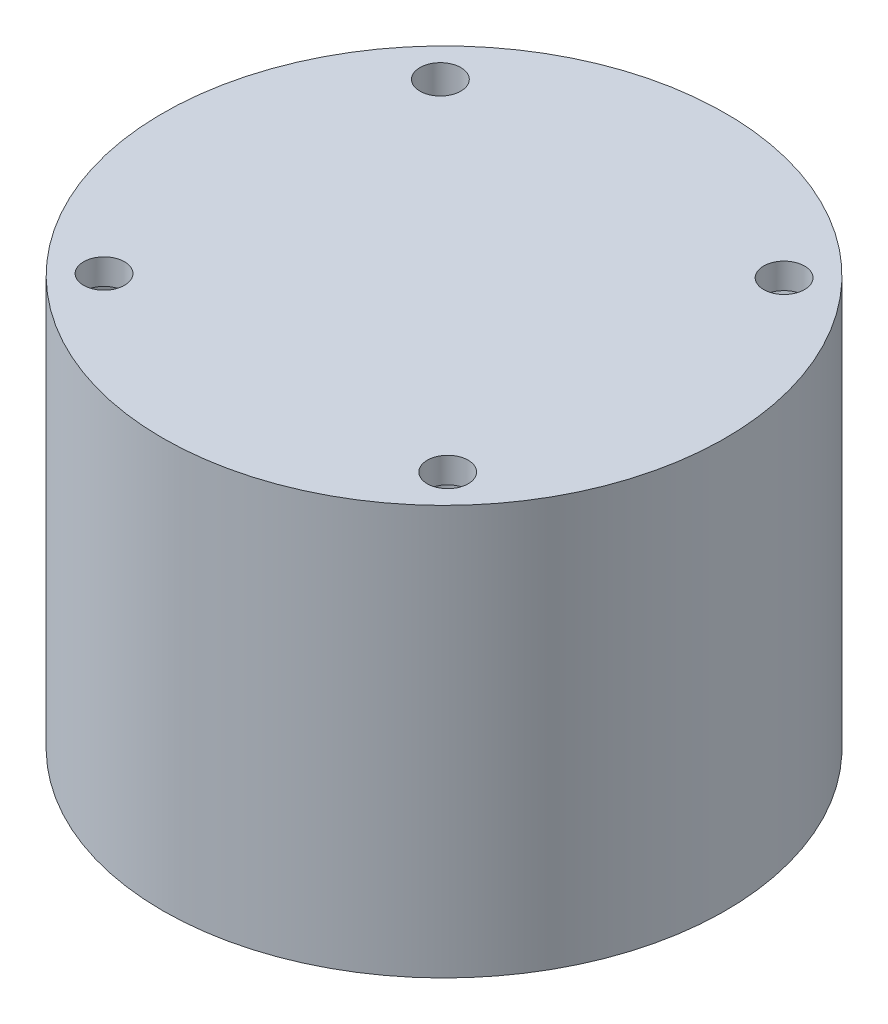
SolidWorks part; units mm, degrees
ref_plane "Спереди" through (0, 0, 0) normal (0, 0, 1) x (1, 0, 0)
ref_plane "Сверху" through (0, 0, 0) normal (0, 1, 0) x (1, 0, 0)
ref_plane "Справа" through (0, 0, 0) normal (1, 0, 0) x (0, 0, -1)
sketch "Эскиз1" plane through (0, 0, 0) normal (0, 1, 0) x (1, 0, 0)
  circle A0 centre (0, 0) radius 55
  dimension "D1" = 110
extrude "Бобышка-Вытянуть1" add sketch "Эскиз1" along normal blind 80
sketch "Эскиз2" plane through (0, 0, 0) normal (0, -1, 0) x (1, 0, 0)
  circle A0 centre (0, 0) radius 50
  dimension "D1" = 100
extrude "Вырез-Вытянуть1" cut sketch "Эскиз2" against normal blind 75
sketch "Эскиз3" plane through (0, 75, 0) normal (0, -1, 0) x (1, 0, 0)
  line L1 (-16.75, -7.5) -> (16.75, -7.5)
  line L2 (-16.75, -7.5) -> (-16.75, 7.5)
  line L3 (-16.75, 7.5) -> (16.75, 7.5)
  line L4 (16.75, -7.5) -> (16.75, 7.5)
  line L5 (-16.75, -7.5) -> (16.75, 7.5) construction
  line L6 (-16.75, 7.5) -> (16.75, -7.5) construction
  point P0 (0, 0)
  dimension "D1" = 15
  dimension "D2" = 33.5
extrude "Вырез-Вытянуть2" cut sketch "Эскиз3" against normal through all
sketch "Эскиз4" plane through (0, 80, 0) normal (0, 1, 0) x (1, 0, 0)
  line L0 (-16.75, 20.5) -> (-16.75, -20.5) construction
  line L1 (-16.75, -20.5) -> (16.75, -20.5) construction
  line L2 (16.75, -20.5) -> (16.75, 20.5) construction
  line L3 (16.75, 20.5) -> (-16.75, 20.5) construction
  line L4 (-23.35, 22.85) -> (23.35, 22.85) construction
  line L5 (16.75, -20.5) -> (-16.75, 20.5) construction
  line L6 (16.75, 20.5) -> (-16.75, -20.5) construction
  line L7 (23.35, 22.85) -> (23.35, -22.85) construction
  line L8 (39.3095, -38.4677) -> (-39.3095, 38.4677) construction
  line L9 (23.35, -22.85) -> (-23.35, -22.85) construction
  line L10 (-23.35, -22.85) -> (-23.35, 22.85) construction
  line L11 (16.75, 7.5) -> (16.75, -7.5) construction
  line L13 (23.35, -22.85) -> (-23.35, 22.85) construction
  line L14 (-16.75, -7.5) -> (-16.75, 7.5) construction
  line L15 (39.3095, 38.4677) -> (-39.3095, -38.4677) construction
  line L16 (23.35, 22.85) -> (-23.35, -22.85) construction
  circle A0 centre (-16.75, 20.5) radius 1.5 construction
  circle A1 centre (16.75, 20.5) radius 1.5 construction
  circle A2 centre (-16.75, -20.5) radius 1.5 construction
  circle A3 centre (16.75, -20.5) radius 1.5 construction
  circle A4 centre (0, 0) radius 55 construction
  circle A5 centre (33.5917, -32.8724) radius 4
  circle A6 centre (-33.5917, -32.8724) radius 4
  circle A7 centre (-33.5917, 32.8724) radius 4
  circle A8 centre (33.5917, 32.8724) radius 4
  point P0 (0, 0)
  point P5 (0, 0)
  point P27 (-16.75, 0)
  point P29 (16.75, 0)
  point P33 (-16.75, 0)
  dimension "D3" = 3
  dimension "D4" = 8
  dimension "D1" = 46.7
  dimension "D2" = 41
  dimension "D5" = 8
  dimension "D6" = 8
  dimension "D7" = 8
  dimension "D8" = 8
  dimension "D9" = 45.7
  dimension "D10" = 33.5
extrude "Вырез-Вытянуть3" cut sketch "Эскиз4" against normal through all
sketch "Sketch2" plane through (0, 80, 0) normal (0, 1, 0) x (1, 0, 0)
  line L1 (16.75, -7.5) -> (-16.75, -7.5)
  line L2 (16.75, -7.5) -> (16.75, 7.5)
  line L3 (16.75, 7.5) -> (-16.75, 7.5)
  line L4 (-16.75, -7.5) -> (-16.75, 7.5)
  line L5 (16.75, -7.5) -> (-16.75, 7.5) construction
  line L6 (16.75, 7.5) -> (-16.75, -7.5) construction
  point P0 (0, 0)
extrude "Boss-Extrude1" add sketch "Sketch2" against normal up to surface (5 mm away) up to face at (0, 75, 0)
